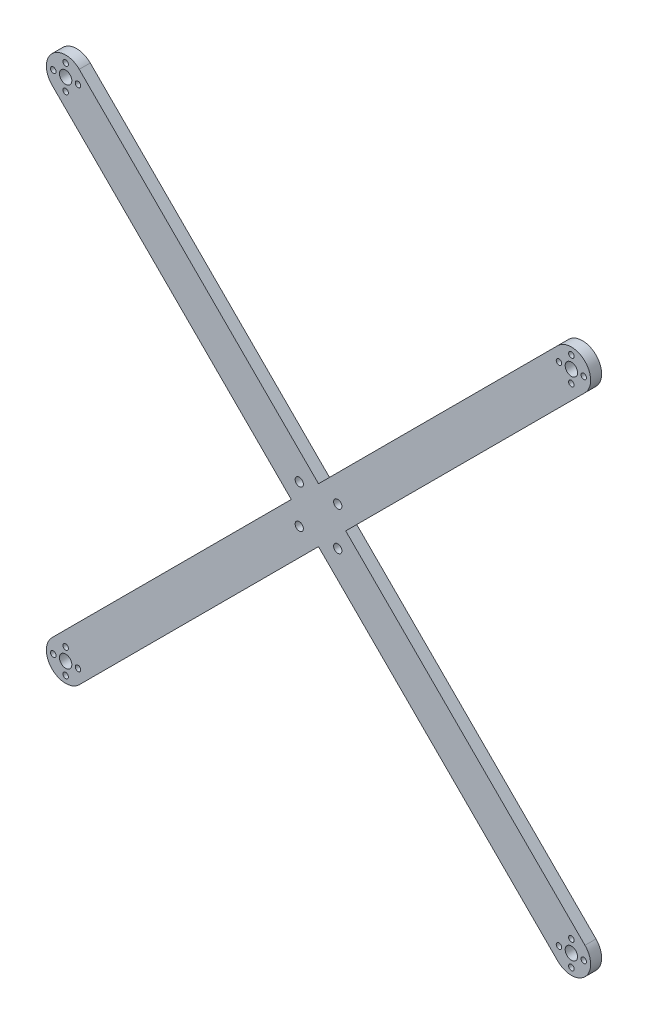
SolidWorks part; units mm, degrees
ref_plane "Alzado" through (0, 0, 0) normal (0, 0, 1) x (1, 0, 0)
ref_plane "Planta" through (0, 0, 0) normal (0, 1, 0) x (1, 0, 0)
ref_plane "Vista lateral" through (0, 0, 0) normal (1, 0, 0) x (0, 0, -1)
sketch "Croquis1" plane through (0, 0, 0) normal (0, 0, 1) x (1, 0, 0)
  line L0 (0, 0) -> (14, 0) construction
  line L1 (0, 0) -> (28, 0)
  line L2 (0, 0) -> (0, 28)
  line L3 (0, 28) -> (28, 28)
  line L4 (28, 0) -> (28, 28)
  line L5 (14, 0) -> (7, 0) construction
  line L6 (7, 0) -> (7, 28) construction
  line L7 (7, 28) -> (14, 28) construction
  line L8 (14, 28) -> (28, 28) construction
  line L9 (21, 28) -> (21, 0) construction
  line L10 (28, 0) -> (28, 14) construction
  line L11 (28, 14) -> (28, 7) construction
  line L12 (28, 7) -> (0, 7) construction
  line L13 (0, 7) -> (0, 14) construction
  line L14 (0, 14) -> (0, 28) construction
  line L15 (0, 21) -> (28, 21) construction
  line L16 (0, 14) -> (28, 14) construction
  line L17 (14, 14) -> (105.9239, 105.9239) construction
  line L18 (14, 14) -> (-77.9239, -77.9239) construction
  line L19 (14, 14) -> (105.9239, -77.9239) construction
  line L20 (14, 14) -> (-77.9239, 105.9239) construction
  line L21 (9.0503, 9.0503) -> (100.9741, -82.8736)
  line L22 (18.9497, 18.9497) -> (110.8736, -72.9741)
  line L23 (18.9497, 9.0503) -> (110.8736, 100.9741)
  line L24 (9.0503, 18.9497) -> (100.9741, 110.8736)
  line L25 (18.9497, 18.9497) -> (-72.9741, 110.8736)
  line L26 (9.0503, 9.0503) -> (-82.8736, 100.9741)
  line L27 (9.0503, 18.9497) -> (-82.8736, -72.9741)
  line L28 (18.9497, 9.0503) -> (-72.9741, -82.8736)
  circle A0 centre (7, 21) radius 1.5
  circle A1 centre (7, 7) radius 1.5
  circle A2 centre (21, 7) radius 1.5
  circle A3 centre (21, 21) radius 1.5
  circle A4 centre (-77.9239, -77.9239) radius 7
  circle A5 centre (105.9239, -77.9239) radius 7
  circle A6 centre (105.9239, 105.9239) radius 7
  circle A7 centre (-77.9239, 105.9239) radius 7
  circle A8 centre (-77.9239, -77.9239) radius 4.5
  circle A9 centre (-73.4239, -77.9239) radius 1
  circle A10 centre (-77.9239, -73.4239) radius 1
  circle A11 centre (-82.4239, -77.9239) radius 1
  circle A12 centre (-77.9239, -82.4239) radius 1.0049
  circle A13 centre (105.9239, -77.9239) radius 4.5
  circle A14 centre (101.4239, -77.9239) radius 1
  circle A15 centre (105.9239, -73.4239) radius 1
  circle A16 centre (110.4239, -77.9239) radius 1
  circle A17 centre (105.9239, -82.4239) radius 1
  circle A18 centre (105.9239, 105.9239) radius 4.5
  circle A19 centre (105.9239, 101.4239) radius 1
  circle A20 centre (110.4239, 105.9239) radius 1
  circle A21 centre (105.9239, 110.4239) radius 1
  circle A22 centre (101.4239, 105.9239) radius 1
  circle A23 centre (-77.9239, 105.9239) radius 4.5
  circle A24 centre (-77.9239, 110.4239) radius 1
  circle A25 centre (-73.4239, 105.9239) radius 1
  circle A26 centre (-77.9239, 101.4239) radius 1
  circle A27 centre (-82.4239, 105.9239) radius 1
  circle A28 centre (-77.9239, -77.9239) radius 2.25
  circle A29 centre (105.9239, -77.9239) radius 2.25
  circle A30 centre (105.9239, 105.9239) radius 2.25
  circle A31 centre (-77.9239, 105.9239) radius 2.25
  dimension "D3" = 130
  dimension "D7" = 7
  dimension "D1" = 28
  dimension "D2" = 28
  dimension "D4" = 130
  dimension "D5" = 130
  dimension "D6" = 130
  dimension "D8" = 7
  dimension "D9" = 7
  dimension "D10" = 7
  dimension "D11" = 7
  dimension "D12" = 7
  dimension "D13" = 7
  dimension "D14" = 7
extrude "Saliente-Extruir1" add sketch "Croquis1" along normal blind 4 contours L28 L23 L22 L25 L24 L27 L26 L21 | L23 L28 L21 L1 L4 L22 A2 | A5 L22 L4 L1 L21 | L25 L22 L23 L4 L3 L24 A3 | L28 L21 L26 L27 L2 L1 A1 | L27 L24 L25 L3 L2 L26 A0 | A4 L28 L1 L2 L27 | A6 L24 L3 L4 L23 | A7 L26 L2 L3 L25 | A22 A18 A19 A20 A21 | A6 A22 A18 A21 A20 A19 | A5 A17 A13 A14 A15 A16 | A17 A13 A16 A15 A14 | A4 A12 A8 A11 A10 A9 | A12 A8 A9 A10 A11 | A27 A23 A26 A25 A24 | A7 A27 A23 A24 A25 A26
